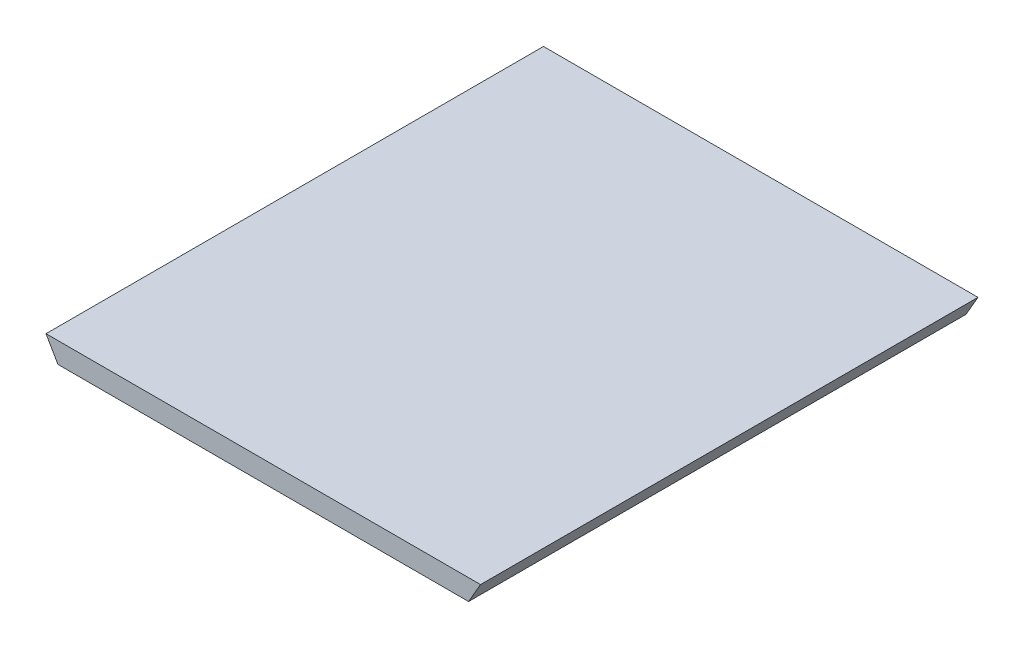
SolidWorks part; units mm, degrees
ref_plane "Front Plane" through (0, 0, 0) normal (0, 0, 1) x (1, 0, 0)
ref_plane "Top Plane" through (0, 0, 0) normal (0, 1, 0) x (1, 0, 0)
ref_plane "Right Plane" through (0, 0, 0) normal (1, 0, 0) x (0, 0, -1)
sketch "Sketch1" plane through (0, 0, 0) normal (0, 0, 1) x (1, 0, 0)
  line L0 (-14.9, 0) -> (14.9, 0)
  line L1 (14.9, 0) -> (15.766, 1.5)
  line L2 (15.766, 1.5) -> (-15.766, 1.5)
  line L3 (-15.766, 1.5) -> (-14.9, 0)
  dimension "D1" = 60
  dimension "D2" = 60
  dimension "D3" = 1.5
  dimension "D4" = 29.8
extrude "Boss-Extrude1" add sketch "Sketch1" along normal blind 36.1
